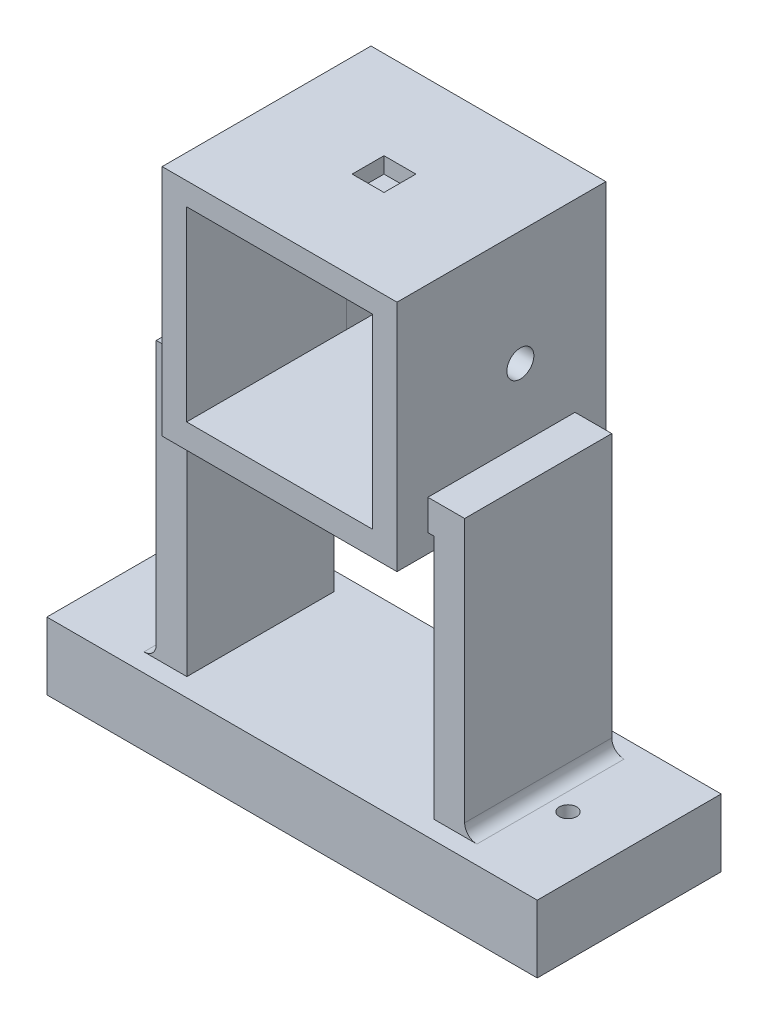
SolidWorks part; units mm, degrees
ref_plane "Front Plane" through (0, 0, 0) normal (0, 0, 1) x (1, 0, 0)
ref_plane "Top Plane" through (0, 0, 0) normal (0, 1, 0) x (1, 0, 0)
ref_plane "Right Plane" through (0, 0, 0) normal (1, 0, 0) x (0, 0, -1)
sketch "Sketch2" plane through (0, 0, 0) normal (0, 0, 1) x (1, 0, 0)
  line L0 (-5.08, -5.08) -> (43.58, -5.08)
  line L1 (0, 0) -> (38.5, 0) construction
  line L2 (0, 0) -> (0, 38.2) construction
  line L3 (0, 38.2) -> (38.5, 38.2) construction
  line L4 (38.5, 0) -> (38.5, 38.2) construction
  line L5 (43.58, -5.08) -> (43.58, 43.28)
  line L6 (-5.08, 43.28) -> (43.58, 43.28)
  line L7 (-5.08, -5.08) -> (-5.08, 43.28)
  dimension "D1" = 38.5
  dimension "D2" = 38.2
  dimension "D3" = 5.08
extrude "Boss-Extrude1" add sketch "Sketch2" along normal blind 43.2689
sketch "Sketch3" plane through (0, 0, 0) normal (0, 0, -1) x (-1, 0, 0)
  line L0 (-43.58, -5.08) -> (-43.58, 43.28) construction
  line L1 (0, 0) -> (-37.992, 0)
  line L2 (0, 0) -> (0, 8.128)
  line L3 (0, 8.128) -> (-37.992, 8.128)
  line L4 (-37.992, 0) -> (-37.992, 8.128)
  dimension "D1" = 5.588
  dimension "D2" = 8.128
extrude "Cut-Extrude1" cut sketch "Sketch3" against normal blind 38.1889
sketch "Sketch4" plane through (0, 0, 43.2689) normal (0, 0, 1) x (1, 0, 0)
  line L0 (43.58, -5.08) -> (43.58, 43.28) construction
  line L1 (-0.0064, 38.608) -> (38.5, 38.608)
  line L2 (-0.0064, 38.608) -> (-0.0064, 0)
  line L3 (-0.0064, 0) -> (38.5, 0)
  line L4 (38.5, 38.608) -> (38.5, 0)
  line L5 (-5.08, -5.08) -> (43.58, -5.08) construction
  dimension "D1" = 38.5064
  dimension "D2" = 38.608
  dimension "D3" = 5.08
  dimension "D4" = 5.08
extrude "Cut-Extrude2" cut sketch "Sketch4" against normal blind 33.1089
sketch "Sketch6" plane through (38.5, 0, 0) normal (-1, 0, 0) x (0, 0, 1)
  circle A0 centre (17.7143, 19.508) radius 2.794
  dimension "D1" = 5.588
extrude "Cut-Extrude3" cut sketch "Sketch6" against normal blind 23.622 and the other way blind 78.486
sketch "Sketch7" plane through (43.58, 0, 0) normal (1, 0, 0) x (0, 0, -1)
  line L0 (-21.6345, -5.08) -> (-21.6345, 14.9944) construction
  line L1 (-43.2689, -5.08) -> (0, -5.08) construction
  line L3 (-36.8745, 5.08) -> (-6.3945, 5.08)
  line L4 (-36.8745, 5.08) -> (-36.8744, -1.27)
  line L5 (-36.8744, -1.27) -> (-6.3945, -1.27)
  line L6 (-6.3945, 5.08) -> (-6.3945, -1.27)
  line L7 (-36.8745, 5.08) -> (-6.3945, -1.27) construction
  line L8 (-36.8744, -1.27) -> (-6.3945, 5.08) construction
  point P4 (-21.6345, 1.905)
  dimension "D1" = 3.81
  dimension "D2" = 6.35
  dimension "D3" = 30.48
extrude "Boss-Extrude2" add sketch "Sketch7" along normal blind 7.62
sketch "Sketch9" plane through (0, 0, 36.8744) normal (0, 0, 1) x (1, 0, 0)
  line L1 (51.2, -1.27) -> (44.85, -1.27)
  line L2 (51.2, -1.27) -> (51.2, -52.07)
  line L3 (51.2, -52.07) -> (44.85, -52.07)
  line L4 (44.85, -1.27) -> (44.85, -52.07)
  dimension "D1" = 6.35
  dimension "D2" = 50.8
extrude "Boss-Extrude3" add sketch "Sketch9" against normal blind 30.48
ref_plane "Plane1" through (19.25, 0, 0) normal (1, 0, 0) x (0, 0, -1)
mirror "Mirror1" about plane through (19.25, 0, 0) normal (1, 0, 0) of "Boss-Extrude3", "Boss-Extrude2"
sketch "Sketch11" plane through (0, -52.07, 0) normal (0, -1, 0) x (1, 0, 0)
  line L0 (-12.7, 21.6345) -> (51.2, 21.6345) construction
  line L1 (-31.55, 40.6844) -> (70.05, 40.6844)
  line L2 (-31.55, 40.6844) -> (-31.55, 2.5844)
  line L3 (-31.55, 2.5844) -> (70.05, 2.5844)
  line L4 (70.05, 40.6844) -> (70.05, 2.5844)
  line L5 (-12.7, 6.3944) -> (-12.7, 36.8744) construction
  line L6 (51.2, 6.3944) -> (51.2, 36.8744) construction
  line L8 (19.25, -23.7979) -> (19.25, 23.7979) construction
  dimension "D1" = 38.1
  dimension "D2" = 19.05
  dimension "D3" = 101.6
  dimension "D4" = 50.8
extrude "Boss-Extrude4" add sketch "Sketch11" along normal blind 13.97
sketch "Sketch14" plane through (0, -66.04, 0) normal (0, -1, 0) x (1, 0, 0)
  line L0 (-31.55, 21.6345) -> (88.8469, 21.6345) construction
  line L1 (-31.55, 40.6844) -> (-31.55, 2.5844) construction
  line L2 (19.25, 2.7133) -> (19.25, 53.7181) construction
  line L3 (19.25, -23.7979) -> (19.25, 23.7979) construction
  circle A0 centre (19.25, 21.6345) radius 38.127 construction
  circle A1 centre (57.377, 21.6344) radius 1.778
  circle A2 centre (-18.877, 21.6344) radius 1.778
  dimension "D1" = 76.254
  dimension "D2" = 3.556
extrude "Cut-Extrude4" cut sketch "Sketch14" against normal up to vertex (13.97 mm away)
fillet "Fillet1" radius 2.54 2 edges at (-12.7, -52.07, 21.6345) (51.2, -52.07, 21.6345)
sketch "Sketch15" plane through (0, 43.28, 0) normal (0, 1, 0) x (1, 0, 0)
  line L1 (-5.08, -21.6345) -> (43.58, -21.6345) construction
  line L2 (-5.08, -43.2689) -> (-5.08, 0) construction
  line L3 (43.58, -43.2689) -> (43.58, 0) construction
  line L4 (19.25, 0) -> (19.25, -43.2689) construction
  line L5 (43.58, 0) -> (-5.08, 0) construction
  line L6 (43.58, -43.2689) -> (-5.08, -43.2689) construction
  line L8 (15.948, -18.3325) -> (22.552, -18.3325)
  line L9 (15.948, -18.3325) -> (15.948, -24.9365)
  line L10 (15.948, -24.9365) -> (22.552, -24.9365)
  line L11 (22.552, -18.3325) -> (22.552, -24.9365)
  line L12 (15.948, -18.3325) -> (22.552, -24.9365) construction
  line L13 (15.948, -24.9365) -> (22.552, -18.3325) construction
  point P12 (19.25, -21.6345)
  dimension "D1" = 6.604
  dimension "D2" = 6.604
extrude "Cut-Extrude5" cut sketch "Sketch15" against normal blind 3.302
